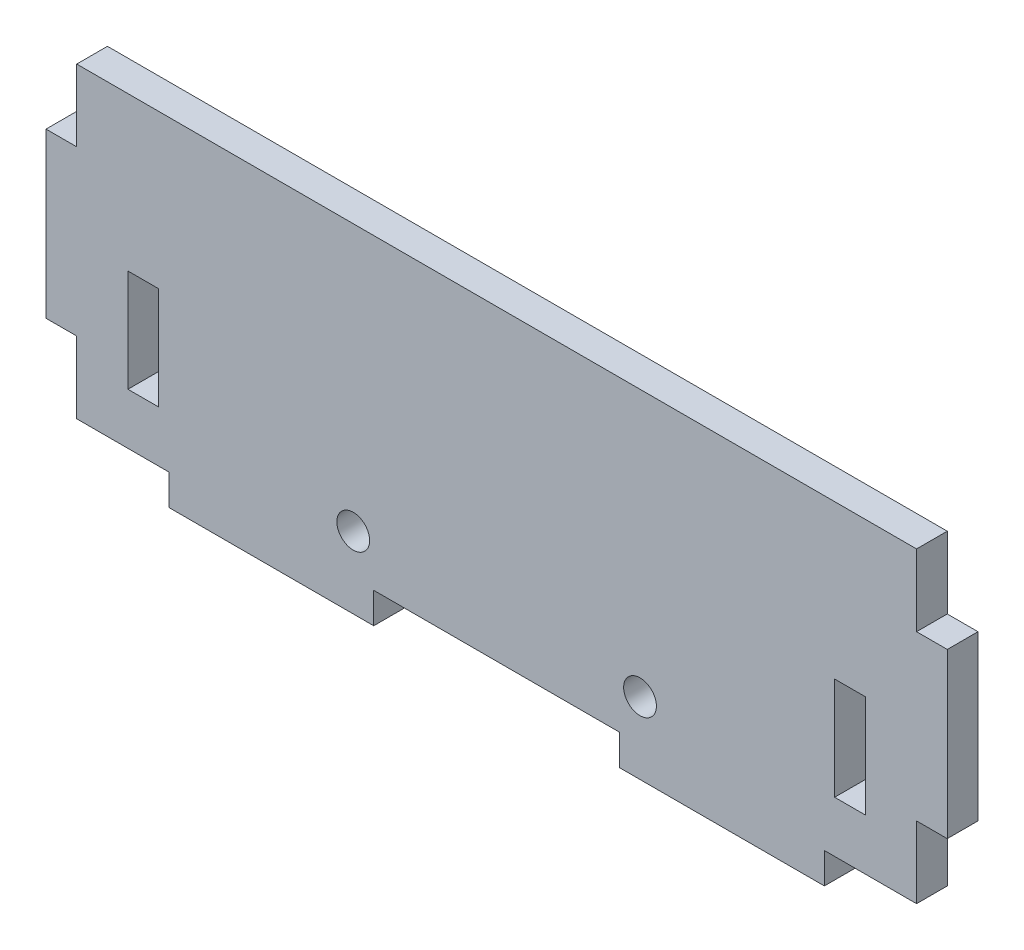
SolidWorks part; units mm, degrees
ref_plane "前视基准面" through (0, 0, 0) normal (0, 0, 1) x (1, 0, 0)
ref_plane "上视基准面" through (0, 0, 0) normal (0, 1, 0) x (1, 0, 0)
ref_plane "右视基准面" through (0, 0, 0) normal (1, 0, 0) x (0, 0, -1)
sketch "草图1" plane through (0, 0, 0) normal (0, 0, 1) x (1, 0, 0)
  line L0 (3, 0) -> (12, 0)
  line L1 (3, 0) -> (12, 0)
  line L2 (0, 7) -> (0, 23)
  line L3 (3, 30) -> (85, 30)
  line L4 (88, 7) -> (88, 23)
  line L5 (12, 0) -> (12, -3)
  line L6 (12, -3) -> (32, -3)
  line L7 (32, -3) -> (32, 0)
  line L8 (85, 0) -> (76, 0)
  line L9 (76, 0) -> (76, -3)
  line L10 (76, -3) -> (56, -3)
  line L11 (56, -3) -> (56, 0)
  line L12 (44, 0) -> (44, 4)
  line L13 (44, 4) -> (55, 4)
  line L14 (55, 4) -> (44, 4)
  line L15 (44, 4) -> (33, 4)
  line L16 (76, 0) -> (85, 0)
  line L17 (85, 0) -> (85, 7)
  line L18 (85, 7) -> (88, 7)
  line L19 (32, 0) -> (56, 0)
  line L20 (88, 23) -> (85, 23)
  line L21 (85, 23) -> (85, 30)
  line L22 (44, 4) -> (30, 4)
  line L23 (0, 23) -> (3, 23)
  line L24 (3, 23) -> (3, 30)
  line L25 (30, 4) -> (55, 4)
  line L26 (3, 0) -> (3, 7)
  line L27 (3, 7) -> (0, 7)
  line L28 (44, 4) -> (58, 4)
  line L29 (3, 15) -> (3, 23)
  line L30 (3, 15) -> (8, 15)
  line L31 (85, 23) -> (85, 15)
  line L32 (8, 15) -> (11, 15)
  line L33 (8, 15) -> (8, 5)
  line L34 (8, 5) -> (11, 5)
  line L35 (11, 15) -> (11, 5)
  line L36 (85, 15) -> (80, 15)
  line L38 (80, 15) -> (77, 15)
  line L39 (80, 15) -> (80, 5)
  line L40 (80, 5) -> (77, 5)
  line L41 (77, 15) -> (77, 5)
  circle A2 centre (30, 4) radius 1.6
  circle A3 centre (58, 4) radius 1.6
extrude "凸台-拉伸1" add sketch "草图1" along normal blind 3
